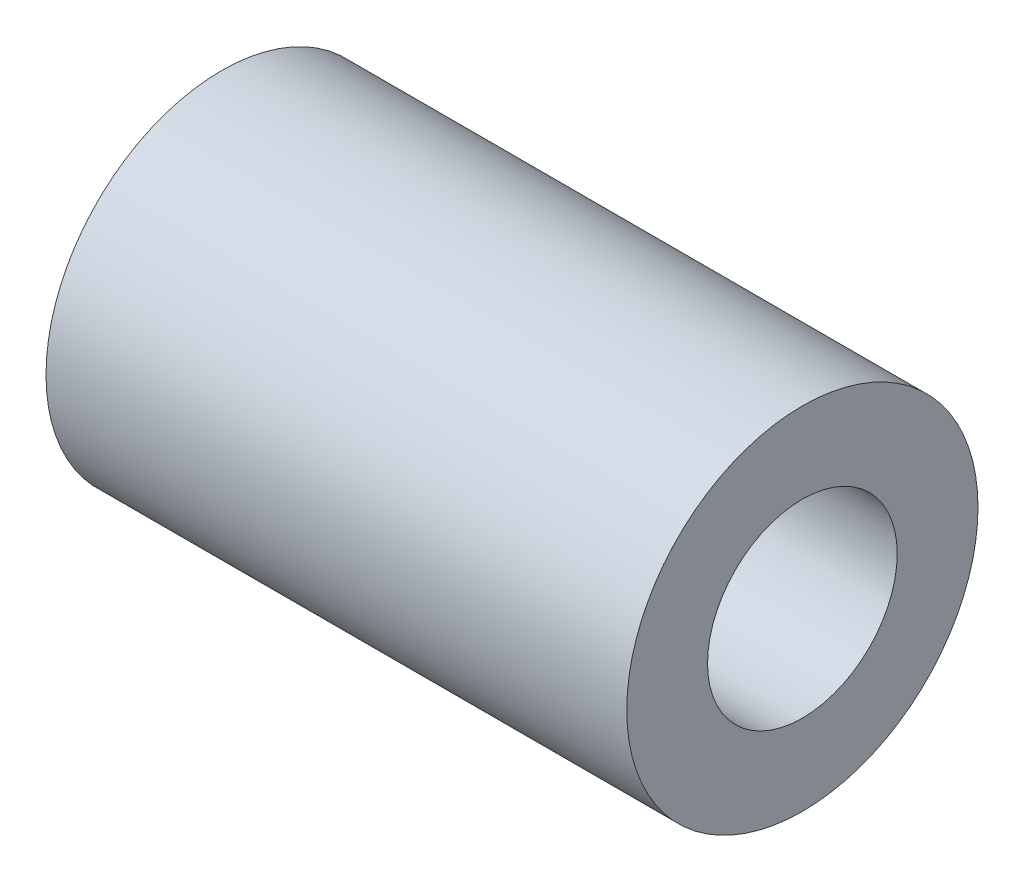
SolidWorks part; units mm, degrees
ref_plane "Plan de face" through (0, 0, 0) normal (0, 0, 1) x (1, 0, 0)
ref_plane "Plan de dessus" through (0, 0, 0) normal (0, 1, 0) x (1, 0, 0)
ref_plane "Plan de droite" through (0, 0, 0) normal (1, 0, 0) x (0, 0, -1)
sketch "Esquisse1" plane through (0, 0, 0) normal (1, 0, 0) x (0, 0, -1)
  circle A0 centre (0, 0) radius 3.429
  circle A1 centre (0, 0) radius 6.35
  dimension "D1" = 6.858
  dimension "D2" = 12.7
extrude "Boss.-Extru.1" add sketch "Esquisse1" against normal blind 21
equation "\"D1@Boss.-Extru.1\"=21mm"
